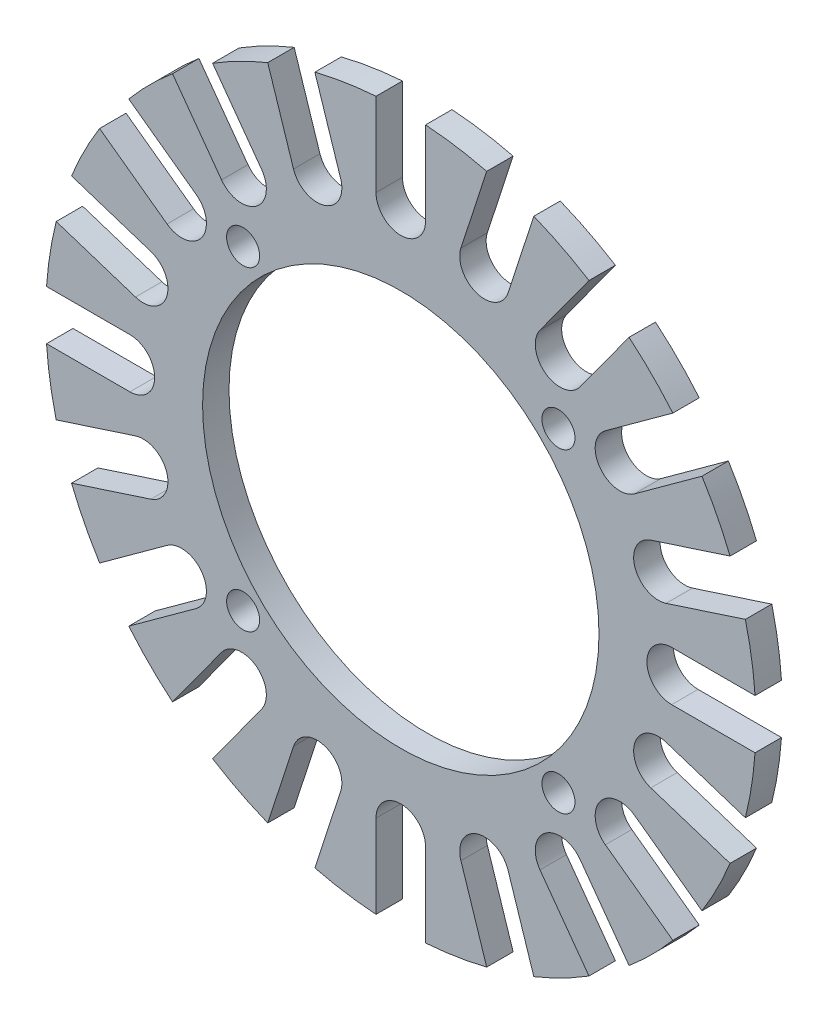
SolidWorks part; units mm, degrees
ref_plane "Front" through (0, 0, 0) normal (0, 0, 1) x (1, 0, 0)
ref_plane "Top" through (0, 0, 0) normal (0, 1, 0) x (1, 0, 0)
ref_plane "Right" through (0, 0, 0) normal (1, 0, 0) x (0, 0, -1)
sketch "Sketch1" plane through (0, 0, 0) normal (0, 0, 1) x (1, 0, 0)
  line L2 (-1.5, 16.4) -> (-1.5, 21.4476)
  line L5 (1.5, 21.4476) -> (1.5, 16.4)
  line L6 (8.0543, 19.9344) -> (6.4945, 15.1338)
  line L7 (3.6413, 16.0609) -> (5.2011, 20.8614)
  line L8 (13.8201, 16.4698) -> (10.8532, 12.3862)
  line L9 (8.4262, 14.1496) -> (11.3931, 18.2332)
  line L10 (18.2332, 11.3931) -> (14.1496, 8.4262)
  line L11 (12.3862, 10.8532) -> (16.4698, 13.8201)
  line L12 (20.8614, 5.2011) -> (16.0609, 3.6413)
  line L13 (15.1338, 6.4945) -> (19.9344, 8.0543)
  line L14 (21.4476, -1.5) -> (16.4, -1.5)
  line L15 (16.4, 1.5) -> (21.4476, 1.5)
  line L16 (19.9344, -8.0543) -> (15.1338, -6.4945)
  line L17 (16.0609, -3.6413) -> (20.8614, -5.2011)
  line L18 (16.4698, -13.8201) -> (12.3862, -10.8532)
  line L19 (14.1496, -8.4262) -> (18.2332, -11.3931)
  line L20 (11.3931, -18.2332) -> (8.4262, -14.1496)
  line L21 (10.8532, -12.3862) -> (13.8201, -16.4698)
  line L22 (5.2011, -20.8614) -> (3.6413, -16.0609)
  line L23 (6.4945, -15.1338) -> (8.0543, -19.9344)
  line L24 (-1.5, -21.4476) -> (-1.5, -16.4)
  line L25 (1.5, -16.4) -> (1.5, -21.4476)
  line L26 (-8.0543, -19.9344) -> (-6.4945, -15.1338)
  line L27 (-3.6413, -16.0609) -> (-5.2011, -20.8614)
  line L28 (-13.8201, -16.4698) -> (-10.8532, -12.3862)
  line L29 (-8.4262, -14.1496) -> (-11.3931, -18.2332)
  line L30 (-18.2332, -11.3931) -> (-14.1496, -8.4262)
  line L31 (-12.3862, -10.8532) -> (-16.4698, -13.8201)
  line L32 (-20.8614, -5.2011) -> (-16.0609, -3.6413)
  line L33 (-15.1338, -6.4945) -> (-19.9344, -8.0543)
  line L34 (-21.4476, 1.5) -> (-16.4, 1.5)
  line L35 (-16.4, -1.5) -> (-21.4476, -1.5)
  line L36 (-19.9344, 8.0543) -> (-15.1338, 6.4945)
  line L37 (-16.0609, 3.6413) -> (-20.8614, 5.2011)
  line L38 (-16.4698, 13.8201) -> (-12.3862, 10.8532)
  line L39 (-14.1496, 8.4262) -> (-18.2332, 11.3931)
  line L40 (-11.3931, 18.2332) -> (-8.4262, 14.1496)
  line L41 (-10.8532, 12.3862) -> (-13.8201, 16.4698)
  line L42 (-5.2011, 20.8614) -> (-3.6413, 16.0609)
  line L43 (-6.4945, 15.1338) -> (-8.0543, 19.9344)
  circle A0 centre (0, 0) radius 12
  circle A2 centre (0, 13.5) radius 1
  circle A5 centre (13.5, 0) radius 1
  circle A6 centre (0, -13.5) radius 1
  circle A7 centre (-13.5, 0) radius 1
  arc A11 (-1.5, 16.4) -> (1.5, 16.4) centre (0, 16.4) ccw
  arc A12 (-1.5, 21.4476) -> (-5.2011, 20.8614) centre (0, 0) ccw
  arc A13 (3.6413, 16.0609) -> (6.4945, 15.1338) centre (5.0679, 15.5973) ccw
  arc A14 (8.4262, 14.1496) -> (10.8532, 12.3862) centre (9.6397, 13.2679) ccw
  arc A15 (12.3862, 10.8532) -> (14.1496, 8.4262) centre (13.2679, 9.6397) ccw
  arc A16 (15.1338, 6.4945) -> (16.0609, 3.6413) centre (15.5973, 5.0679) ccw
  arc A17 (16.4, 1.5) -> (16.4, -1.5) centre (16.4, 0) ccw
  arc A18 (16.0609, -3.6413) -> (15.1338, -6.4945) centre (15.5973, -5.0679) ccw
  arc A19 (14.1496, -8.4262) -> (12.3862, -10.8532) centre (13.2679, -9.6397) ccw
  arc A20 (10.8532, -12.3862) -> (8.4262, -14.1496) centre (9.6397, -13.2679) ccw
  arc A21 (6.4945, -15.1338) -> (3.6413, -16.0609) centre (5.0679, -15.5973) ccw
  arc A22 (1.5, -16.4) -> (-1.5, -16.4) centre (0, -16.4) ccw
  arc A23 (-3.6413, -16.0609) -> (-6.4945, -15.1338) centre (-5.0679, -15.5973) ccw
  arc A24 (-8.4262, -14.1496) -> (-10.8532, -12.3862) centre (-9.6397, -13.2679) ccw
  arc A25 (-12.3862, -10.8532) -> (-14.1496, -8.4262) centre (-13.2679, -9.6397) ccw
  arc A26 (-15.1338, -6.4945) -> (-16.0609, -3.6413) centre (-15.5973, -5.0679) ccw
  arc A27 (-16.4, -1.5) -> (-16.4, 1.5) centre (-16.4, 0) ccw
  arc A28 (-16.0609, 3.6413) -> (-15.1338, 6.4945) centre (-15.5973, 5.0679) ccw
  arc A29 (-14.1496, 8.4262) -> (-12.3862, 10.8532) centre (-13.2679, 9.6397) ccw
  arc A30 (-10.8532, 12.3862) -> (-8.4262, 14.1496) centre (-9.6397, 13.2679) ccw
  arc A31 (-6.4945, 15.1338) -> (-3.6413, 16.0609) centre (-5.0679, 15.5973) ccw
  arc A32 (-8.0543, 19.9344) -> (-11.3931, 18.2332) centre (0, 0) ccw
  arc A33 (5.2011, 20.8614) -> (1.5, 21.4476) centre (0, 0) ccw
  arc A34 (11.3931, 18.2332) -> (8.0543, 19.9344) centre (0, 0) ccw
  arc A35 (16.4698, 13.8201) -> (13.8201, 16.4698) centre (0, 0) ccw
  arc A36 (19.9344, 8.0543) -> (18.2332, 11.3931) centre (0, 0) ccw
  arc A37 (21.4476, 1.5) -> (20.8614, 5.2011) centre (0, 0) ccw
  arc A38 (20.8614, -5.2011) -> (21.4476, -1.5) centre (0, 0) ccw
  arc A39 (18.2332, -11.3931) -> (19.9344, -8.0543) centre (0, 0) ccw
  arc A40 (13.8201, -16.4698) -> (16.4698, -13.8201) centre (0, 0) ccw
  arc A41 (8.0543, -19.9344) -> (11.3931, -18.2332) centre (0, 0) ccw
  arc A42 (1.5, -21.4476) -> (5.2011, -20.8614) centre (0, 0) ccw
  arc A43 (-5.2011, -20.8614) -> (-1.5, -21.4476) centre (0, 0) ccw
  arc A44 (-11.3931, -18.2332) -> (-8.0543, -19.9344) centre (0, 0) ccw
  arc A45 (-16.4698, -13.8201) -> (-13.8201, -16.4698) centre (0, 0) ccw
  arc A46 (-19.9344, -8.0543) -> (-18.2332, -11.3931) centre (0, 0) ccw
  arc A47 (-21.4476, -1.5) -> (-20.8614, -5.2011) centre (0, 0) ccw
  arc A48 (-20.8614, 5.2011) -> (-21.4476, 1.5) centre (0, 0) ccw
  arc A49 (-13.8201, 16.4698) -> (-16.4698, 13.8201) centre (0, 0) ccw
  arc A50 (-18.2332, 11.3931) -> (-19.9344, 8.0543) centre (0, 0) ccw
  dimension "D1" = 4
  dimension "D2" = 20
extrude "Boss-Extrude1" add sketch "Sketch1" along normal blind 1.6
sketch "Sketch2" plane through (0, 0, 1.6) normal (0, 0, 1) x (1, 0, 0)
  circle A0 centre (0, 0) radius 12
  circle A1 centre (0, 0) radius 14.9
extrude "Boss-Extrude2" add sketch "Sketch2" against normal up to surface (1.6 mm away) up to face at (0, 0, 0)
sketch "Sketch3" plane through (0, 0, 1.6) normal (0, 0, 1) x (1, 0, 0)
  circle A1 centre (9.5459, 9.5459) radius 1
  circle A2 centre (9.5459, -9.5459) radius 1
  circle A3 centre (-9.5459, -9.5459) radius 1
  circle A4 centre (-9.5459, 9.5459) radius 1
  dimension "D1" = 4
extrude "Cut-Extrude1" cut sketch "Sketch3" against normal blind 10
